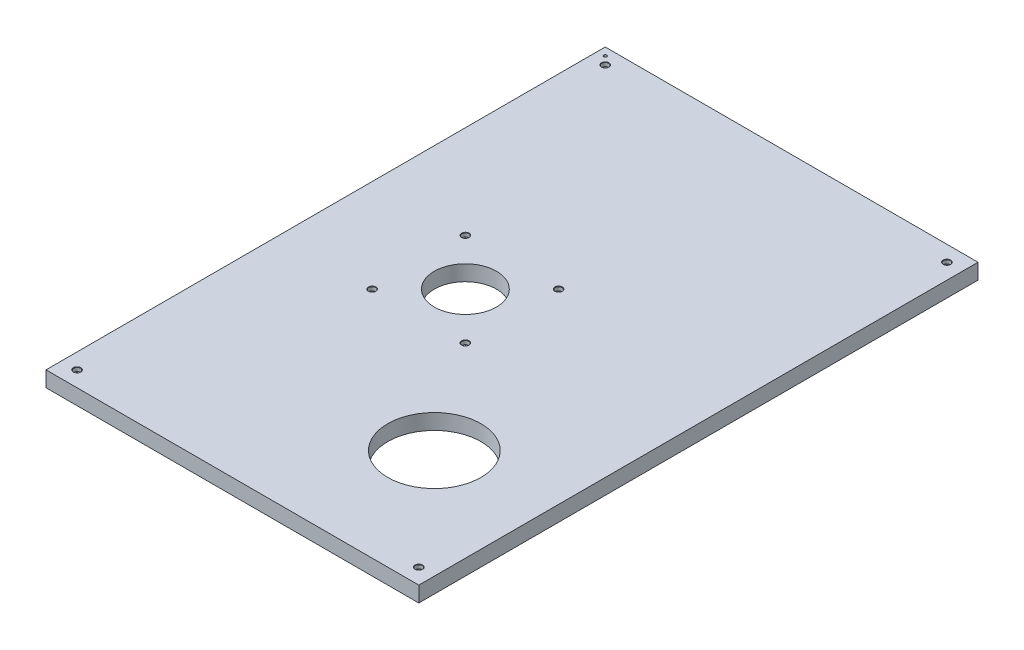
SolidWorks part; units mm, degrees
ref_plane "Front" through (0, 0, 0) normal (0, 0, 1) x (1, 0, 0)
ref_plane "Top" through (0, 0, 0) normal (0, 1, 0) x (1, 0, 0)
ref_plane "Right" through (0, 0, 0) normal (1, 0, 0) x (0, 0, -1)
sketch "Sketch2" plane through (0, 0, 0) normal (0, 1, 0) x (1, 0, 0)
  line L1 (354.2885, 449.2317) -> (963.8885, 449.2317)
  line L2 (354.2885, 449.2317) -> (354.2885, -465.1683)
  line L3 (354.2885, -465.1683) -> (963.8885, -465.1683)
  line L4 (963.8885, 449.2317) -> (963.8885, -465.1683)
  dimension "D1" = 914.4
  dimension "D2" = 609.6
extrude "Boss-Extrude1" add sketch "Sketch2" along normal blind 25.4
sketch "Sketch38" plane through (0, 25.4, 0) normal (0, 1, 0) x (1, 0, 0)
  line L0 (366.9885, 449.2317) -> (366.9885, 124.8403) construction
  line L1 (963.8885, 449.2317) -> (354.2885, 449.2317) construction
  line L2 (354.2885, 436.5317) -> (-59.3928, 436.5317) construction
  line L3 (354.2885, 449.2317) -> (354.2885, -465.1683) construction
  line L4 (354.2885, -465.1683) -> (963.8885, -465.1683) construction
  line L6 (506.6885, -84.1683) -> (659.0885, -84.1683)
  line L7 (506.6885, -84.1683) -> (506.6885, 68.2317)
  line L8 (506.6885, 68.2317) -> (659.0885, 68.2317)
  line L9 (659.0885, -84.1683) -> (659.0885, 68.2317)
  line L10 (506.6885, -84.1683) -> (659.0885, 68.2317) construction
  line L11 (506.6885, 68.2317) -> (659.0885, -84.1683) construction
  circle A0 centre (582.8885, -7.9683) radius 50.8
  circle A1 centre (786.0885, -261.9683) radius 63.5
  circle A2 centre (582.8885, -7.9683) radius 215.9
  dimension "D3" = 101.6
  dimension "D8" = 127
  dimension "D9" = 431.8
  dimension "D1" = 12.7
  dimension "D2" = 12.7
  dimension "D4" = 457.2
  dimension "D5" = 228.6
  dimension "D6" = 254
  dimension "D7" = 203.2
  dimension "D10" = 152.4
  dimension "D11" = 152.4
hole_wizard "1/4-20 Tapped Hole1" positions "Sketch54" profile "Sketch53" tap size "1/4-20" standard "ANSI Inch" end condition through all
sketch "Sketch54" plane through (0, 25.4, 0) normal (0, 1, 0) x (1, 0, 0)
  line L0 (366.9885, 449.2317) -> (366.9885, 124.8403) construction
  point P0 (366.9885, 436.5317)
sketch "Sketch53" plane through (366.9885, 25.4, -436.5317) normal (1, 0, 0) x (0, 0, 1)
  line L0 (0, 0) -> (0, 25.4)
  line L1 (0, 25.4) -> (2.5527, 25.4)
  line L2 (2.5527, 25.4) -> (2.5527, 0)
  line L5 (2.5527, 0) -> (0, 0)
  line L11 (0, -6.35) -> (0, 107.95) construction
  dimension "Thru Tap Drill Dia." = 5.1054
  dimension "Thru Tap Drill Depth" = 25.4
cosmetic thread "Hole Thread1" parameters "D2"=6.35
pattern_linear "LPattern1" [suppressed] count 24 spacing 25.4 along (-1, 0, 0) count 36 spacing 25.4 along (0, 0, 1)
sketch "Sketch48" plane through (0, 25.4, 0) normal (0, 1, 0) x (1, 0, 0)
  line L1 (-268.918, 449.2317) -> (1001.082, 449.2317)
  line L2 (-268.918, 449.2317) -> (-268.918, -465.1683)
  line L3 (-268.918, -465.1683) -> (1001.082, -465.1683)
  line L4 (1001.082, 449.2317) -> (1001.082, -465.1683)
  dimension "D1" = 914.4
  dimension "D2" = 1270
  dimension "D3" = 457.2
sketch "Sketch46" plane through (0, 25.4, 0) normal (0, 1, 0) x (1, 0, 0)
  circle A0 centre (786.0885, -261.9683) radius 76.2
  dimension "D1" = 152.4
extrude "Cut-Extrude3" cut sketch "Sketch46" against normal through all
sketch "Sketch47" plane through (0, 25.4, 0) normal (0, 1, 0) x (1, 0, 0)
  circle A0 centre (582.8885, -7.9683) radius 50.8
extrude "Cut-Extrude4" cut sketch "Sketch47" against normal through all
hole_wizard "CBORE for 1/4 Socket Head Cap Screw1" positions "Sketch52" profile "Sketch51" counterbore size "1/4" standard "ANSI Inch" end condition through all
sketch "Sketch52" plane through (0, 25.4, 0) normal (0, 1, 0) x (1, 0, 0)
  line L0 (-268.918, 449.2317) -> (1001.082, 449.2317) construction
  line L1 (354.2885, 449.2317) -> (354.2885, -465.1683) construction
  line L2 (963.8885, -465.1683) -> (963.8885, 449.2317) construction
  line L3 (-268.918, -465.1683) -> (1001.082, -465.1683) construction
  point P0 (379.6885, 423.8317)
  point P2 (938.4885, 423.8317)
  point P4 (938.4885, -439.7683)
  point P6 (379.6885, -439.7683)
  point P8 (506.6885, -84.1683)
  point P11 (659.0885, -84.1683)
  point P14 (659.0885, 68.2317)
  point P17 (506.6885, 68.2317)
  dimension "D1" = 25.4
  dimension "D2" = 25.4
  dimension "D3" = 25.4
  dimension "D4" = 25.4
  dimension "D5" = 25.4
  dimension "D6" = 25.4
  dimension "D7" = 25.4
  dimension "D8" = 25.4
sketch "Sketch51" plane through (379.6885, 25.4, -423.8317) normal (1, 0, 0) x (0, 0, 1)
  line L0 (0, 0) -> (0, 25.4)
  line L1 (0, 25.4) -> (3.3782, 25.4)
  line L3 (3.3782, 25.4) -> (3.3782, 6.35)
  line L4 (5.5562, 6.35) -> (3.3782, 6.35)
  line L5 (5.5562, 6.35) -> (5.5562, 0.635)
  line L6 (5.5562, 0.635) -> (6.1912, 0)
  line L7 (6.1912, 0) -> (0, 0)
  line L8 (-5.5562, 0.635) -> (-6.1912, 0) construction
  line L11 (0, -6.35) -> (0, 107.95) construction
  dimension "Thru Hole Dia." = 6.7564
  dimension "Thru Hole Depth" = 25.4
  dimension "C'Bore Dia." = 11.1125
  dimension "C'Bore Depth" = 6.35
  dimension "Near C'Sink Dia." = 12.3825
  dimension "Near C'Sink Angle" = 90
